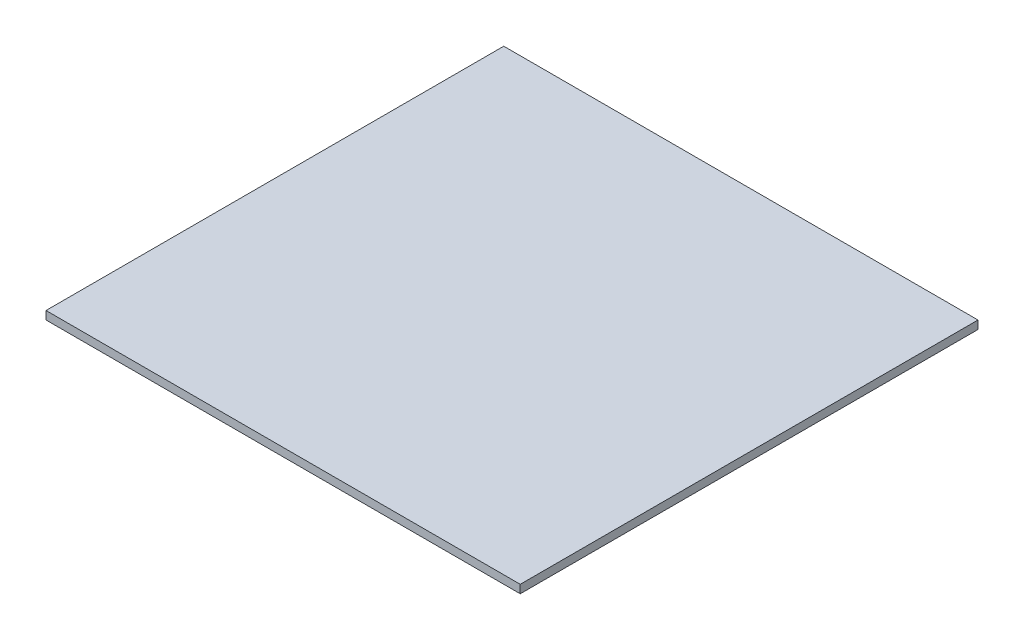
SolidWorks part; units mm, degrees
ref_plane "前视基准面" through (0, 0, 0) normal (0, 0, 1) x (1, 0, 0)
ref_plane "上视基准面" through (0, 0, 0) normal (0, 1, 0) x (1, 0, 0)
ref_plane "右视基准面" through (0, 0, 0) normal (1, 0, 0) x (0, 0, -1)
sketch "草图1" plane through (0, 0, 0) normal (0, 1, 0) x (1, 0, 0)
  line L1 (0, 0) -> (103.6, 0)
  line L2 (0, 0) -> (0, 100)
  line L3 (0, 100) -> (103.6, 100)
  line L4 (103.6, 0) -> (103.6, 100)
  dimension "D1" = 103.6
  dimension "D2" = 100
extrude "凸台-拉伸1" add sketch "草图1" along normal blind 1.8
